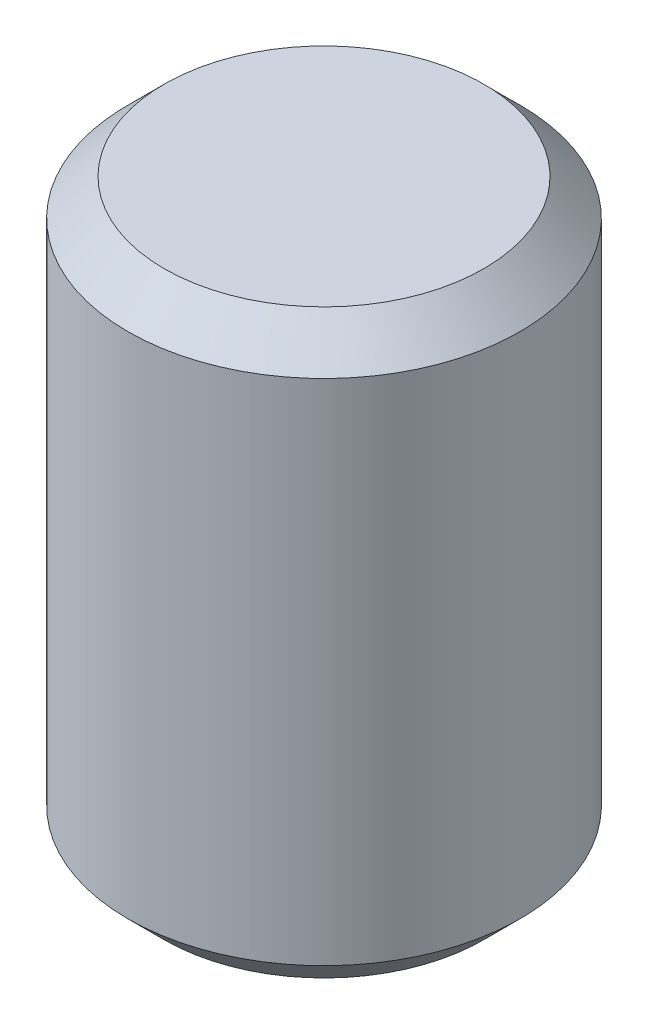
SolidWorks part; units mm, degrees
ref_plane "Front Plane" through (0, 0, 0) normal (0, 0, 1) x (1, 0, 0)
ref_plane "Top Plane" through (0, 0, 0) normal (0, 1, 0) x (1, 0, 0)
ref_plane "Right Plane" through (0, 0, 0) normal (1, 0, 0) x (0, 0, -1)
sketch "Sketch1" plane through (0, 0, 0) normal (0, 1, 0) x (1, 0, 0)
  circle A0 centre (0, 0) radius 1.35
  dimension "2.7" = 2.7
extrude "Boss-Extrude1" add sketch "Sketch1" along normal blind 4
chamfer "Chamfer1" distance 0.25 angle 45 2 edges at (0, 4, 1.35) (0, 0, 1.35)
